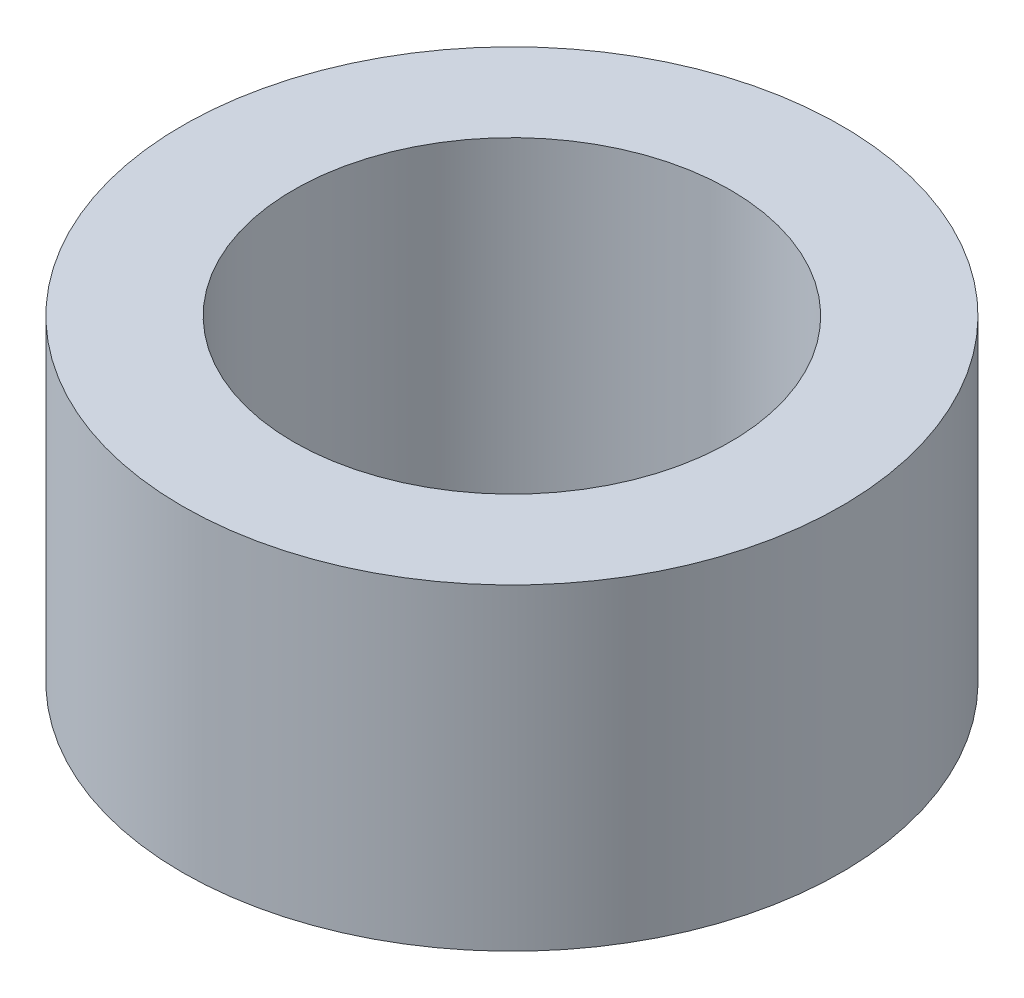
SolidWorks part; units mm, degrees
ref_plane "Front Plane" through (0, 0, 0) normal (0, 0, 1) x (1, 0, 0)
ref_plane "Top Plane" through (0, 0, 0) normal (0, 1, 0) x (1, 0, 0)
ref_plane "Right Plane" through (0, 0, 0) normal (1, 0, 0) x (0, 0, -1)
sketch "Sketch1" plane through (0, 0, 0) normal (0, 1, 0) x (1, 0, 0)
  circle A0 centre (0, 0) radius 4
  circle A1 centre (0, 0) radius 2.65
  dimension "D1" = 8
  dimension "D2" = 5.3
extrude "Boss-Extrude1" add sketch "Sketch1" along normal blind 3.85
